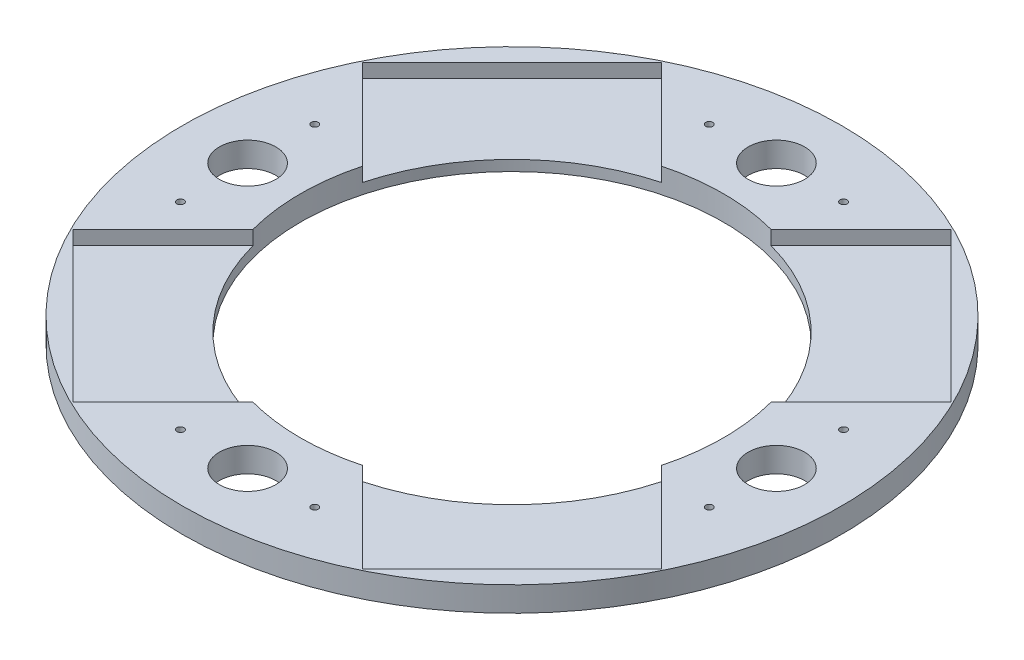
SolidWorks part; units mm, degrees
material "AISI 304"
ref_plane "前视基准面" through (0, 0, 0) normal (0, 0, 1) x (1, 0, 0)
ref_plane "上视基准面" through (0, 0, 0) normal (0, 1, 0) x (1, 0, 0)
ref_plane "右视基准面" through (0, 0, 0) normal (1, 0, 0) x (0, 0, -1)
sketch "Sketch2" plane through (0, 0, 0) normal (0, 1, 0) x (1, 0, 0)
  circle A0 centre (0, 0) radius 93.4851
extrude "Extrude1" add sketch "Sketch2" along normal blind 7
sketch "Sketch3" plane through (0, 7, 0) normal (0, 1, 0) x (1, 0, 0)
  circle A0 centre (0, 75) radius 8
  dimension "D1" = 75
extrude "Cut-Extrude1" cut sketch "Sketch3" against normal through all
sketch "Sketch6" plane through (0, 7, 0) normal (0, 1, 0) x (1, 0, 0)
  circle A0 centre (0, 75) radius 8 construction
  point P0 (0, 75)
hole_wizard "#3-48 Tapped Hole1" positions "Sketch4" profile "Sketch5" tap size "#3-48" standard "ANSI Inch" end condition through all
sketch "Sketch4" plane through (0, 7, 0) normal (0, 1, 0) x (1, 0, 0)
  circle A0 centre (0, 75) radius 8 construction
  point P0 (-19.05, 75)
  point P2 (19.05, 75)
  dimension "D1" = 38.1
  dimension "D2" = 19.05
sketch "Sketch5" plane through (-19.05, 7, -75) normal (1, 0, 0) x (0, 0, 1)
  line L0 (0, 0) -> (0, 7)
  line L1 (0, 7) -> (0.9969, 7)
  line L2 (0.9969, 7) -> (0.9969, 0)
  line L5 (0.9969, 0) -> (0, 0)
  line L11 (0, -6.35) -> (0, 107.95) construction
  dimension "Thru Tap Drill Dia." = 1.9939
  dimension "Thru Tap Drill Depth" = 7
cosmetic thread "Hole Thread1" parameters "D2"=2.5146
cosmetic thread "Hole Thread2" parameters "D2"=2.5146
pattern_circular "CirPattern1" count 4 over 360 about axis through (0, 0, 0) along (0, 1, 0) of "#3-48 Tapped Hole1", "Cut-Extrude1"
sketch "Sketch7" plane through (0, 7, 0) normal (0, 1, 0) x (1, 0, 0)
  line L0 (0, 75) -> (75, 0) construction
sketch "Sketch8" plane through (0, 7, 0) normal (0, 1, 0) x (1, 0, 0)
  circle A0 centre (0, 0) radius 60
extrude "Cut-Extrude2" cut sketch "Sketch8" against normal through all
ref_plane "Plane1" through (-47.025, 0, -47.025) normal (0.7071, 0, 0.7071) x (0.7071, 0, -0.7071)
sketch "Sketch9" plane through (0, 7, 0) normal (0, 1, 0) x (1, 0, 0)
  line L1 (42.4596, -0.0332) -> (-0.0332, -42.3932)
  line L6 (-0.0332, -42.3932) -> (41.0442, -83.4706)
  line L7 (41.0442, -83.4706) -> (83.4706, -41.0442)
  line L8 (83.4706, -41.0442) -> (42.4596, -0.0332)
  line L11 (0, 75) -> (75, 0) construction
  line L12 (0, 0) -> (21.2132, -21.2132)
  circle M1 centre (0, 0) radius 60
  dimension "D1" = 30
  dimension "D2" = 60
extrude "Cut-Extrude10" cut sketch "Sketch9" against normal blind 4 contours L7 L8 L1 L6 M1
pattern_circular "CirPattern4" count 4 over 360 about axis through (0, 0, 0) along (0, 1, 0) of "Cut-Extrude10"
